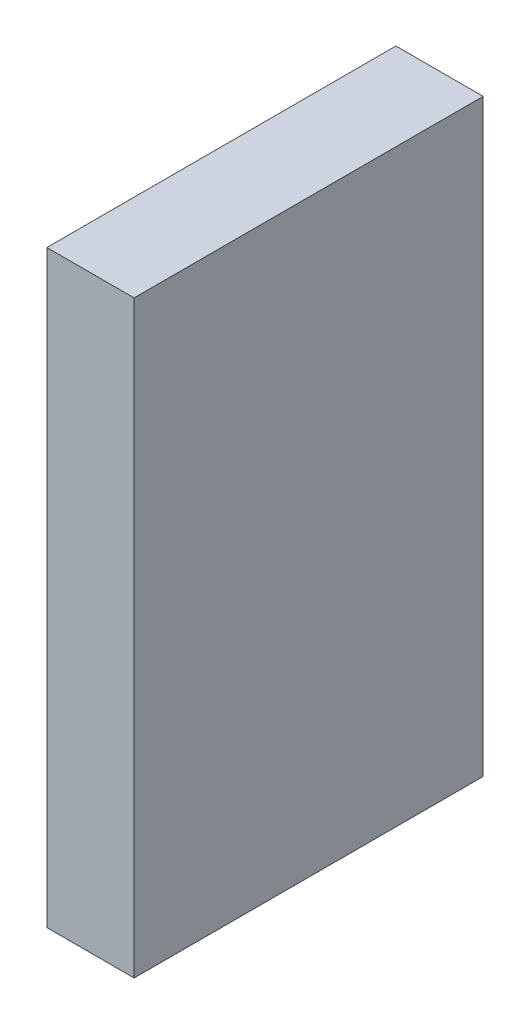
SolidWorks part; units mm, degrees
material "Epoxy, Unfilled"
ref_plane "Front Plane" through (0, 0, 0) normal (0, 0, 1) x (1, 0, 0)
ref_plane "Top Plane" through (0, 0, 0) normal (0, 1, 0) x (1, 0, 0)
ref_plane "Right Plane" through (0, 0, 0) normal (1, 0, 0) x (0, 0, -1)
sketch "Sketch2" plane through (0, 0, 0) normal (1, 0, 0) x (0, 0, -1)
  line L1 (-4, -6.75) -> (4, -6.75)
  line L2 (-4, -6.75) -> (-4, 6.75)
  line L3 (-4, 6.75) -> (4, 6.75)
  line L4 (4, -6.75) -> (4, 6.75)
  line L5 (-4, -6.75) -> (4, 6.75) construction
  line L6 (-4, 6.75) -> (4, -6.75) construction
  point P0 (0, 0)
  dimension "D1" = 8
  dimension "D2" = 13.5
extrude "Boss-Extrude1" add sketch "Sketch2" along normal blind 2
sketch "Sketch5" plane through (0, 0, 0) normal (-1, 0, 0) x (0, 0, 1)
  point P0 (0, 0)
